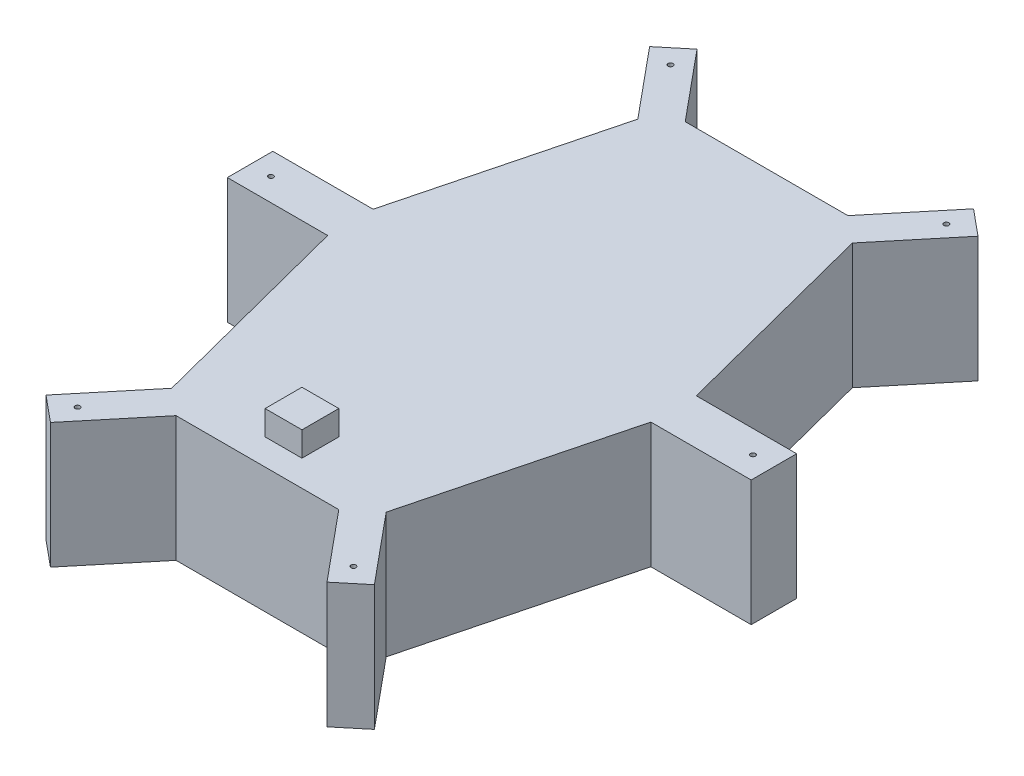
SolidWorks part; units mm, degrees
ref_plane "前视基准面" through (0, 0, 0) normal (0, 0, 1) x (1, 0, 0)
ref_plane "上视基准面" through (0, 0, 0) normal (0, 1, 0) x (1, 0, 0)
ref_plane "右视基准面" through (0, 0, 0) normal (1, 0, 0) x (0, 0, -1)
sketch "草图1" plane through (0, 0, 0) normal (0, 1, 0) x (1, 0, 0)
  line L1 (43.65, -94.8429) -> (65.75, -9.25)
  line L3 (65.75, 9.25) -> (43.65, 94.8429)
  line L5 (33.1, 103.5829) -> (-33.1, 103.5829)
  line L7 (-43.65, 94.8429) -> (-65.75, 9.25)
  line L9 (-65.75, -9.25) -> (-43.65, -94.8429)
  line L11 (-33.1, -103.5829) -> (33.1, -103.5829)
  line L12 (-43.65, 94.8429) -> (-66.8096, 122.7987)
  line L13 (-66.8096, 122.7987) -> (-56.2596, 131.5387)
  line L14 (-56.2596, 131.5387) -> (-33.1, 103.5829)
  line L16 (56.2596, 131.5387) -> (33.1, 103.5829)
  line L17 (66.8096, 122.7987) -> (56.2596, 131.5387)
  line L18 (43.65, 94.8429) -> (66.8096, 122.7987)
  line L20 (43.65, -94.8429) -> (66.8096, -122.7987)
  line L21 (66.8096, -122.7987) -> (56.2596, -131.5387)
  line L22 (56.2596, -131.5387) -> (33.1, -103.5829)
  line L23 (-56.2596, -131.5387) -> (-33.1, -103.5829)
  line L24 (-66.8096, -122.7987) -> (-56.2596, -131.5387)
  line L25 (-43.65, -94.8429) -> (-66.8096, -122.7987)
  line L26 (-65.75, 9.25) -> (-106.5676, 9.25)
  line L28 (-106.5676, 9.25) -> (-106.5676, -9.25)
  line L29 (-65.75, -9.25) -> (-106.5676, -9.25)
  line L30 (106.5676, 9.25) -> (106.5676, -9.25)
  line L31 (65.75, -9.25) -> (106.5676, -9.25)
  line L33 (65.75, 9.25) -> (106.5676, 9.25)
  point P24 (0, 0)
  point P26 (0, 0)
  point P29 (-63.8149, -9.25)
extrude "凸台-拉伸1" add sketch "草图1" along normal blind 51 contours L11 L22 L21 L20 L1 L31 L30 L33 L3 L18 L17 L16 L5 L14 L13 L12 L7 L26 L28 L29 L9 L25 L24 L23
sketch "草图2" plane through (0, 0, 0) normal (0, -1, 0) x (1, 0, 0)
  circle A0 centre (98.0676, 0) radius 1
  point P5 (96.1485, -9.25)
  point P7 (0, 0)
  point P11 (98.0676, 0)
  point P13 (0, 0)
  point P14 (0, 0)
extrude "切除-拉伸1" cut sketch "草图2" against normal up to next (51 mm away)
mirror "镜向1" about plane through (0, 0, 0) normal (1, 0, 0) of "切除-拉伸1"
sketch "草图3" plane through (0, 0, 0) normal (0, -1, 0) x (1, 0, 0)
  circle A0 centre (56.1119, 120.6231) radius 1
  point P6 (56.1119, 120.6231)
extrude "切除-拉伸2" cut sketch "草图3" against normal up to next (51 mm away)
mirror "镜向2" about plane through (0, 0, 0) normal (1, 0, 0) of "切除-拉伸2"
mirror "镜向3" about plane through (0, 0, 0) normal (0, 0, 1) of "切除-拉伸2", "镜向2"
sketch "草图4" plane through (0, 51, 0) normal (0, -1, 0) x (1, 0, 0)
  line L3 (-7.5, 77.9627) -> (7.5, 77.9627)
  line L4 (-7.5, 77.9627) -> (-7.5, 92.9627)
  line L5 (-7.5, 92.9627) -> (7.5, 92.9627)
  line L6 (7.5, 77.9627) -> (7.5, 92.9627)
  line L7 (-7.5, 77.9627) -> (7.5, 92.9627) construction
  line L8 (-7.5, 92.9627) -> (7.5, 77.9627) construction
extrude "凸台-拉伸2" add sketch "草图4" against normal blind 10
